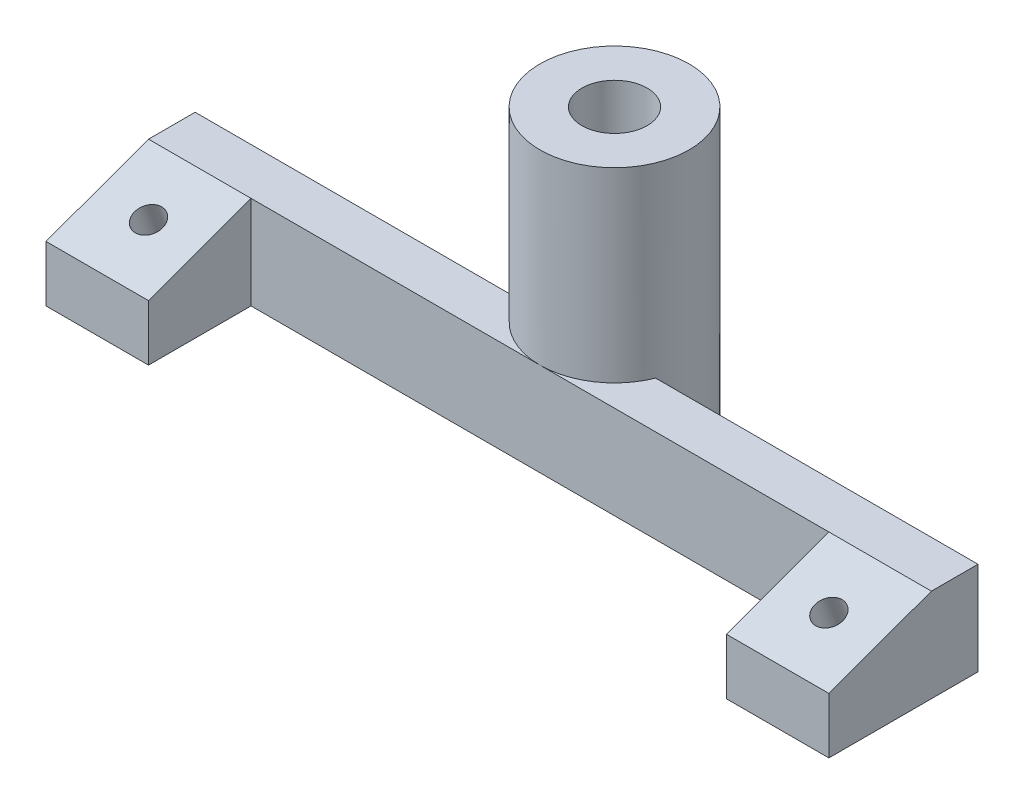
SolidWorks part; units mm, degrees
ref_plane "前视基准面" through (0, 0, 0) normal (0, 0, 1) x (1, 0, 0)
ref_plane "上视基准面" through (0, 0, 0) normal (0, 1, 0) x (1, 0, 0)
ref_plane "右视基准面" through (0, 0, 0) normal (1, 0, 0) x (0, 0, -1)
other "Configuration Table"
sketch "草图1" plane through (0, 0, 0) normal (0, 1, 0) x (1, 0, 0)
  line L0 (-42, 5.5) -> (-42, 10.5)
  line L1 (-31, 5.5) -> (31, 5.5)
  line L2 (-42, 5.5) -> (-42, -5.5)
  line L3 (-42, -5.5) -> (-31, -5.5)
  line L4 (42, 5.5) -> (42, -5.5)
  line L5 (-42, 5.5) -> (42, -5.5) construction
  line L6 (-42, -5.5) -> (42, 5.5) construction
  line L8 (-42, 10.5) -> (42, 10.5)
  line L9 (42, 10.5) -> (42, 5.5)
  line L12 (-31, 5.5) -> (-31, -5.5)
  line L13 (31, -5.5) -> (42, -5.5)
  line L14 (31, 5.5) -> (31, -5.5)
  point P0 (0, 0)
extrude "凸台-拉伸1" add sketch "草图1" along normal blind 10
sketch "草图5" plane through (-42, 0, 0) normal (-1, 0, 0) x (0, 0, 1)
  line L0 (-5.5, 10) -> (5.5, 5.9963)
  line L3 (-5.5, 10) -> (5.5, 10)
  line L4 (5.5, 10) -> (5.5, 5.9963)
extrude "切除-拉伸4" cut sketch "草图5" against normal through all
sketch "草图6" plane through (0, 13.1503, -14.1554) normal (0, -0.9397, -0.342) x (1, 0, 0)
  circle A0 centre (-36.5, 15.0639) radius 1.5
  circle A1 centre (36.5, 15.0639) radius 1.5
extrude "切除-拉伸5" cut sketch "草图6" along normal through all
ref_plane "基准面2" through (0, 3.3038, 1.2025) normal (0, 0.9397, 0.342) x (1, 0, 0)
sketch "草图7" plane through (0, 3.3038, 1.2025) normal (0, 0.9397, 0.342) x (1, 0, 0)
  circle A0 centre (-36.5, 2.7355) radius 3.25
  circle A1 centre (36.5, 2.7355) radius 3.25
extrude "切除-拉伸6" cut sketch "草图7" against normal through all
sketch "草图8" plane through (0, 0, 0) normal (0, -1, 0) x (1, 0, 0)
  circle A0 centre (0, -13.5) radius 8
extrude "凸台-拉伸2" add sketch "草图8" against normal blind 30
sketch "草图9" plane through (0, 30, 0) normal (0, 1, 0) x (1, 0, 0)
  circle A0 centre (0, 13.5) radius 3.5
extrude "切除-拉伸7" cut sketch "草图9" against normal blind 30
sketch "草图10" plane through (0, 0, 0) normal (0, -1, 0) x (1, 0, 0)
  circle A0 centre (0, -13.5) radius 5.25
extrude "切除-拉伸8" cut sketch "草图10" against normal blind 24
